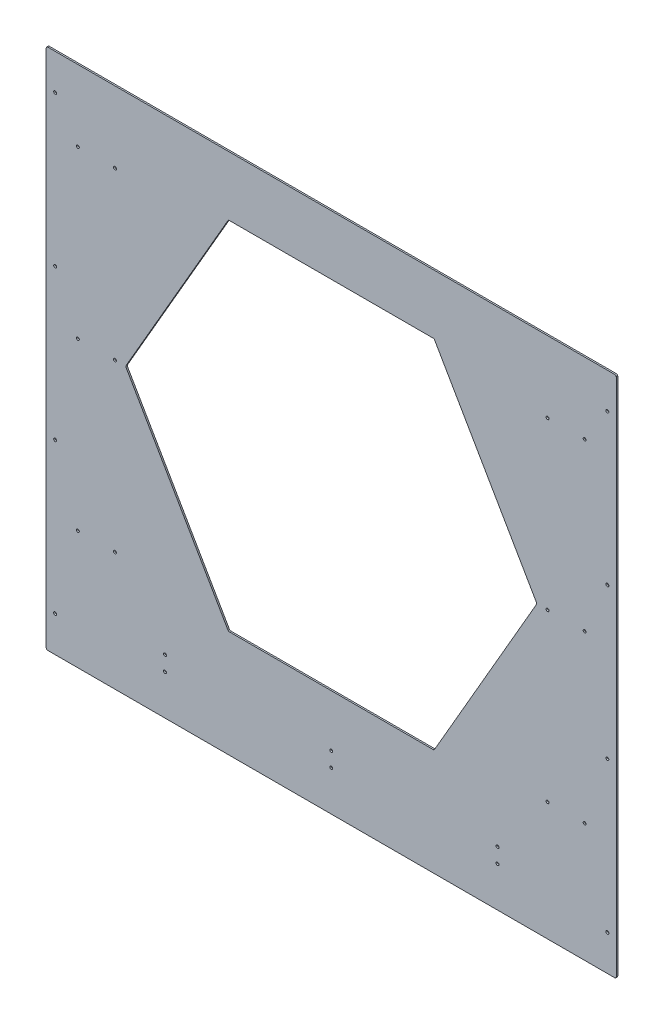
SolidWorks part; units mm, degrees
material "PC High Viscosity"
ref_plane "Front Plane" through (0, 0, 0) normal (0, 0, 1) x (1, 0, 0)
ref_plane "Top Plane" through (0, 0, 0) normal (0, 1, 0) x (1, 0, 0)
ref_plane "Right Plane" through (0, 0, 0) normal (1, 0, 0) x (0, 0, -1)
sketch "Sketch1" plane through (0, 0, 0) normal (0, 0, 1) x (1, 0, 0)
  line L1 (0, 0) -> (1219.2, 0)
  line L2 (0, 0) -> (0, 1016)
  line L3 (0, 1016) -> (1219.2, 1016)
  line L4 (1219.2, 0) -> (1219.2, 1016)
  line L5 (1049.5409, 508) -> (829.5705, 889)
  line L6 (829.5705, 889) -> (389.6295, 889)
  line L7 (389.6295, 889) -> (169.6591, 508)
  line L8 (169.6591, 508) -> (389.6295, 127)
  line L9 (389.6295, 127) -> (829.5705, 127)
  line L10 (829.5705, 127) -> (1049.5409, 508)
  circle A0 centre (609.6, 508) radius 381 construction
  circle A1 centre (609.6, 508) radius 381 construction
  point P7 (1219.2, 508)
  point P8 (609.6, 1016)
  dimension "D3" = 762
  dimension "D1" = 1219.2
  dimension "D2" = 1016
extrude "Boss-Extrude1" add sketch "Sketch1" along normal blind 3.175
hole_wizard "1/4 (0.25) Diameter Hole1" positions "Sketch2" profile "Sketch3" hole size "1/4" standard "ANSI Inch" end condition through all
sketch "Sketch2" plane through (0, 0, 3.175) normal (0, 0, 1) x (1, 0, 0)
  line L0 (0, 508) -> (1219.2, 508) construction
  line L1 (0, 1016) -> (0, 0) construction
  line L2 (1219.2, 0) -> (1219.2, 1016) construction
  line L4 (609.6, 0) -> (609.6, 1016) construction
  line L5 (0, 0) -> (1219.2, 0) construction
  line L6 (1219.2, 1016) -> (0, 1016) construction
  point P0 (254, 15.875)
  point P2 (609.6, 15.875)
  point P4 (965.2, 15.875)
  dimension "D1" = 355.6
  dimension "D2" = 15.875
sketch "Sketch3" plane through (254, 15.875, 3.175) normal (1, 0, 0) x (0, -1, 0)
  line L0 (0, 0) -> (0, 3.175)
  line L1 (0, 3.175) -> (3.175, 3.175)
  line L2 (3.175, 3.175) -> (3.175, 0)
  line L5 (3.175, 0) -> (0, 0)
  line L11 (0, -6.35) -> (0, 107.95) construction
  dimension "Thru Hole Dia." = 6.35
  dimension "Thru Hole Depth" = 3.175
hole_wizard "1/4 (0.25) Diameter Hole2" positions "Sketch4" profile "Sketch5" hole size "1/4" standard "ANSI Inch" end condition through all
sketch "Sketch4" plane through (0, 0, 3.175) normal (0, 0, 1) x (1, 0, 0)
  line L1 (72.39, 1016) -> (142.24, 1016) construction
  line L2 (72.39, 1016) -> (72.39, 0) construction
  line L3 (72.39, 0) -> (142.24, 0) construction
  line L4 (142.24, 1016) -> (142.24, 0) construction
  line L5 (1219.2, 1016) -> (0, 1016) construction
  line L6 (0, 0) -> (1219.2, 0) construction
  line L7 (609.6, 1016) -> (609.6, 0) construction
  line L9 (1219.2, 508) -> (0, 508) construction
  line L10 (1219.2, 0) -> (1219.2, 1016) construction
  line L11 (0, 1016) -> (0, 0) construction
  line L13 (107.315, 1016) -> (107.315, 0) construction
  point P105 (67.6275, 863.6)
  point P107 (147.0025, 863.6)
  point P110 (67.6275, 152.4)
  point P111 (147.0025, 152.4)
  point P112 (67.6275, 508)
  point P114 (147.0025, 508)
  point P119 (1072.1975, 152.4)
  point P120 (1151.5725, 152.4)
  point P121 (1072.1975, 508)
  point P122 (1151.5725, 508)
  point P123 (1072.1975, 863.6)
  point P124 (1151.5725, 863.6)
  point P125 (147.0025, 498.4612)
  point P126 (67.6275, 498.4612)
  point P127 (0, 0)
  point P128 (67.6275, 508)
  point P129 (147.0025, 508)
  dimension "D1" = 934.72
  dimension "D2" = 69.85
  dimension "D3" = 79.375
  dimension "D4" = 355.6
sketch "Sketch5" plane through (1151.5725, 863.6, 3.175) normal (1, 0, 0) x (0, -1, 0)
  line L0 (0, 0) -> (0, 3.175)
  line L1 (0, 3.175) -> (3.175, 3.175)
  line L2 (3.175, 3.175) -> (3.175, 0)
  line L5 (3.175, 0) -> (0, 0)
  line L11 (0, -6.35) -> (0, 107.95) construction
  dimension "Thru Hole Dia." = 6.35
  dimension "Thru Hole Depth" = 3.175
sketch "Sketch7" plane through (0, 0, 3.175) normal (0, 0, 1) x (1, 0, 0)
  line L1 (1219.2, 0) -> (0, 0)
  line L2 (1219.2, 0) -> (1219.2, -101.6)
  line L3 (1219.2, -101.6) -> (0, -101.6)
  line L4 (0, 0) -> (0, -101.6)
  dimension "D1" = 101.6
extrude "Boss-Extrude2" add sketch "Sketch7" against normal up to surface (3.175 mm away) up to face at (70.8025, 863.6, 0)
hole_wizard "1/4 (0.25) Diameter Hole3" positions "Sketch8" profile "Sketch9" hole size "1/4" standard "ANSI Inch" end condition through all
sketch "Sketch8" plane through (0, 0, 3.175) normal (0, 0, 1) x (1, 0, 0)
  line L0 (1219.2, 0) -> (0, 0) construction
  line L1 (1219.2, 0) -> (0, 0)
  circle A0 centre (254, 15.875) radius 3.175 construction
  circle A1 centre (609.6, 15.875) radius 3.175 construction
  circle A2 centre (965.2, 15.875) radius 3.175 construction
  circle A3 centre (254, 15.875) radius 3.175 construction
  circle A4 centre (609.6, 15.875) radius 3.175 construction
  circle A5 centre (965.2, 15.875) radius 3.175 construction
  point P12 (254, -15.875)
  point P13 (609.6, -15.875)
  point P14 (965.2, -15.875)
sketch "Sketch9" plane through (965.2, -15.875, 3.175) normal (1, 0, 0) x (0, -1, 0)
  line L0 (0, 0) -> (0, 3.175)
  line L1 (0, 3.175) -> (3.175, 3.175)
  line L2 (3.175, 3.175) -> (3.175, 0)
  line L5 (3.175, 0) -> (0, 0)
  line L11 (0, -6.35) -> (0, 107.95) construction
  dimension "Thru Hole Dia." = 6.35
  dimension "Thru Hole Depth" = 3.175
fillet "Fillet1" radius 3.175 10 edges at (0, 1016, 1.5875) (1219.2, 1016, 1.5875) (1219.2, -101.6, 1.5875) (0, -101.6, 1.5875) (829.5705, 889, 1.5875) (1049.5409, 508, 1.5875) (389.6295, 889, 1.5875) (169.6591, 508, 1.5875) (389.6295, 127, 1.5875) (829.5705, 127, 1.5875)
hole_wizard "1/4 (0.266) Diameter Hole1" positions "Sketch10" profile "Sketch11" hole size "1/4" standard "ANSI Inch" end condition through all
sketch "Sketch10" plane through (0, 0, 3.175) normal (0, 0, 1) x (1, 0, 0)
  line L0 (609.6, -101.6) -> (609.6, 1016) construction
  line L1 (3.175, -101.6) -> (1216.025, -101.6) construction
  line L2 (1216.025, 1016) -> (3.175, 1016) construction
  line L4 (1219.2, 457.2) -> (0, 457.2) construction
  line L5 (1219.2, -98.425) -> (1219.2, 1012.825) construction
  line L6 (0, 1012.825) -> (0, -98.425) construction
  point P35 (1200.15, 939.8)
  point P46 (1200.15, 618.0667)
  point P47 (1200.15, 296.3333)
  point P48 (1200.15, -25.4)
  point P54 (19.05, 939.8)
  point P55 (19.05, 618.0667)
  point P56 (19.05, -25.4)
  point P57 (19.05, 296.3333)
  dimension "D1" = 4
  dimension "D2" = 76.2
  dimension "D3" = 19.05
sketch "Sketch11" plane through (19.05, 296.3333, 3.175) normal (1, 0, 0) x (0, -1, 0)
  line L0 (0, 0) -> (0, 3.175)
  line L1 (0, 3.175) -> (3.175, 3.175)
  line L2 (3.175, 3.175) -> (3.175, 0)
  line L5 (3.175, 0) -> (0, 0)
  line L11 (0, -6.35) -> (0, 107.95) construction
  dimension "Thru Hole Dia." = 6.35
  dimension "Thru Hole Depth" = 3.175
